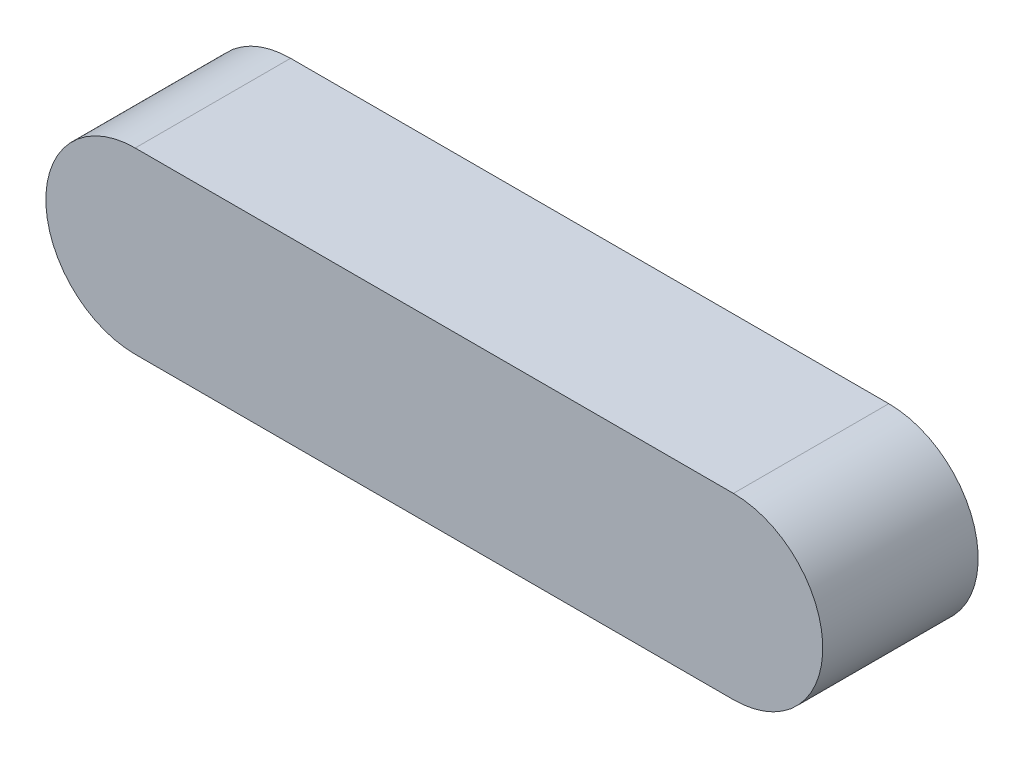
SolidWorks part; units mm, degrees
ref_plane "Front Plane" through (0, 0, 0) normal (0, 0, 1) x (1, 0, 0)
ref_plane "Top Plane" through (0, 0, 0) normal (0, 1, 0) x (1, 0, 0)
ref_plane "Right Plane" through (0, 0, 0) normal (1, 0, 0) x (0, 0, -1)
sketch "Sketch2" plane through (0, 0, 0) normal (0, 0, 1) x (1, 0, 0)
  line L0 (0, 0) -> (77, 0) construction
  line L1 (0, 11.5) -> (77, 11.5)
  line L2 (0, -11.5) -> (77, -11.5)
  arc A0 (0, 11.5) -> (0, -11.5) centre (0, 0) ccw
  arc A1 (77, -11.5) -> (77, 11.5) centre (77, 0) ccw
  point P3 (38.5, 0)
  point P8 (-11.5, 0)
  point P9 (88.5, 0)
  dimension "D1" = 100
  dimension "D2" = 23
extrude "Boss-Extrude1" add sketch "Sketch2" along normal blind 20
sketch "Sketch3" plane through (0, -11.5, 0) normal (0, -1, 0) x (1, 0, 0)
  line L0 (0, 0) -> (77, 0) construction
  circle A0 centre (38.5, 10) radius 3
  dimension "D2" = 6
  dimension "D1" = 10
extrude "Cut-Extrude1" cut sketch "Sketch3" against normal blind 5
